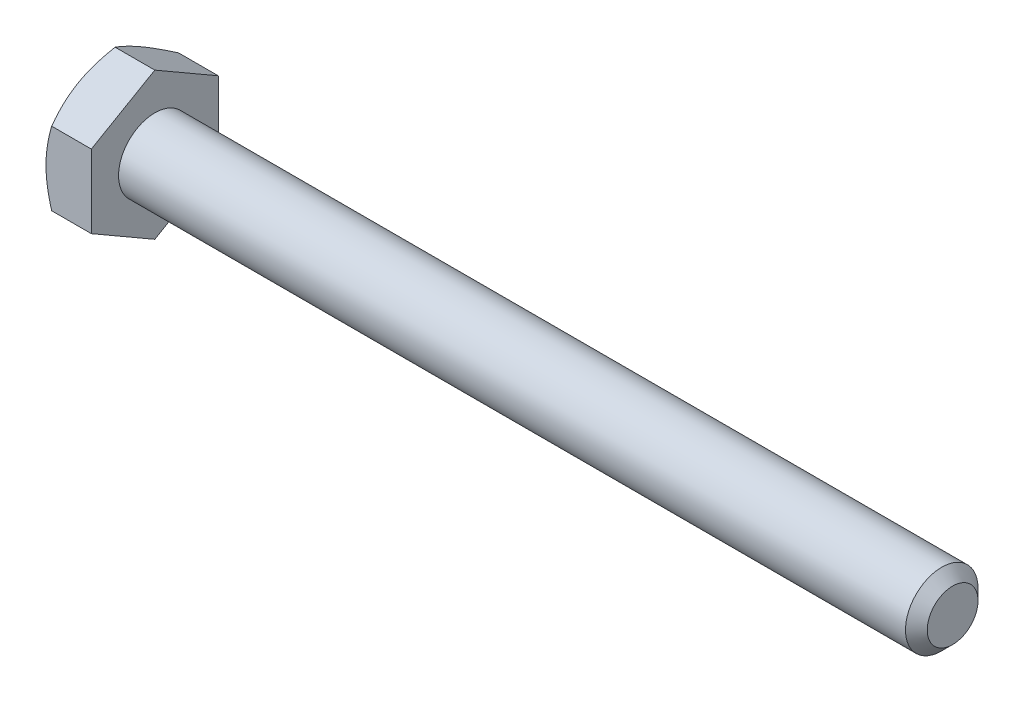
SolidWorks part; units mm, degrees
ref_plane "Front Plane" through (0, 0, 0) normal (0, 0, 1) x (1, 0, 0)
ref_plane "Top Plane" through (0, 0, 0) normal (0, 1, 0) x (1, 0, 0)
ref_plane "Right Plane" through (0, 0, 0) normal (1, 0, 0) x (0, 0, -1)
sketch "Sketch1" plane through (0, 0, 0) normal (0, 0, 1) x (1, 0, 0)
  line L0 (-36.9094, 0) -> (36.9094, 0) construction
  line L1 (36.9094, 3.175) -> (36.9094, -3.175) construction
  line L2 (-32.9406, 5.5562) -> (-32.9406, -5.5562) construction
  line L3 (-36.9094, 5.5562) -> (-36.9094, -5.5562) construction
  point P9 (-32.9406, 0)
  point P10 (32.4644, -3.175)
  dimension "D1" = 4.445
  dimension "Screw Dia" = 6.35
  dimension "Hex" = 11.1125
  dimension "Head Ht" = 3.9688
  dimension "Screw Lenght" = 69.85
ref_plane "Plane2" through (36.9094, 0, 0) normal (1, 0, 0) x (0, 0, -1)
sketch "Sketch5" plane through (36.9094, 0, 0) normal (1, 0, 0) x (0, 0, -1)
  circle A0 centre (0, 0) radius 3.175
extrude "Boss-Extrude3" add sketch "Sketch5" against normal up to vertex (69.85 mm away) up to point (-32.9406, 0, 0)
sketch "Sketch9" plane through (36.9094, 0, 0) normal (1, 0, 0) x (0, 0, -1)
  circle A1 centre (0, 0) radius 3.175
  circle A2 centre (0, 0) radius 3.175
  dimension "D1" = 0
curve "Helix/Spiral1" pitch 1.27 height 20.32 turns 16 parameters "Pitch"=1.27
chamfer "Chamfer1" distance 0.9525 angle 45 1 edges at (36.9094, 0, -3.175)
sketch "Sketch10" plane through (0, 0, 0) normal (0, 0, 1) x (1, 0, 0)
  line L0 (36.9094, 3.175) -> (37.3856, 2.3501)
  line L1 (37.3856, 2.3501) -> (37.5444, 2.3501)
  line L2 (37.5444, 2.3501) -> (38.0206, 3.175)
  line L3 (36.9094, 3.175) -> (38.0206, 3.175)
  line L4 (37.465, 3.175) -> (37.465, 2.3501) construction
  line L5 (37.1475, 2.7626) -> (37.7825, 2.7626) construction
  dimension "D1" = 60
  dimension "D2" = 0.1588
  dimension "D3" = 0.635
sketch "Sketch11" plane through (0, 0, 0) normal (0, 0, 1) x (1, 0, 0)
  line L0 (-32.9406, 3.175) -> (-32.9406, 0)
  line L1 (-32.9406, 0) -> (21.0344, 0)
  line L3 (21.0344, 0) -> (17.8594, 3.175)
  line L4 (-32.9406, 3.175) -> (17.8594, 3.175)
  dimension "D1" = 45
  dimension "MIn Thread" = 19.05
revolve "Revolve1" add sketch "Sketch11" angle 360 about L1
sketch "Sketch6" plane through (-32.9406, 0, 0) normal (-1, 0, 0) x (0, 0, 1)
  line L0 (0, 5.5562) -> (0, -5.5562) construction
  line L1 (5.5563, 3.2079) -> (0, 6.4158)
  line L2 (0, 6.4158) -> (-5.5562, 3.2079)
  line L3 (-5.5562, 3.2079) -> (-5.5562, -3.2079)
  line L4 (-5.5562, -3.2079) -> (0, -6.4158)
  line L5 (0, -6.4158) -> (5.5563, -3.2079)
  line L6 (5.5563, -3.2079) -> (5.5563, 3.2079)
  circle A0 centre (0, 0) radius 5.5563 construction
extrude "Boss-Extrude4" add sketch "Sketch6" along normal up to vertex (3.9688 mm away) up to point (-36.9094, -5.5562, 0)
sketch "Sketch7" plane through (-36.9094, 0, 0) normal (-1, 0, 0) x (0, 0, 1)
  circle A0 centre (0, 0) radius 5.5563 construction
  circle A1 centre (0, 0) radius 5.5563
sketch "Sketch8" plane through (-36.9094, 0, 0) normal (-1, 0, 0) x (0, 0, 1)
  circle A0 centre (0, 0) radius 5.5563 construction
  circle A1 centre (0, 0) radius 5.5563
extrude "Cut-Extrude3" cut sketch "Sketch8" against normal through all draft 60 flip side to cut
sketch "Sketch12" plane through (-36.9094, 0, 0) normal (-1, 0, 0) x (0, 0, 1)
  line L0 (0, 4.2783) -> (0, 2.3892) construction
  line L1 (0.1667, 4.2783) -> (0.1667, 2.3892)
  line L2 (-0.1667, 4.2783) -> (-0.1667, 2.3892)
  line L3 (0, 3.175) -> (0, -3.175) construction
  arc A0 (0.1667, 4.2783) -> (-0.1667, 4.2783) centre (0, 4.2783) ccw
  arc A1 (-0.1667, 2.3892) -> (0.1667, 2.3892) centre (0, 2.3892) ccw
  circle A3 centre (0, 0) radius 2.2225 construction
  circle A4 centre (0, 0) radius 4.445 construction
  point P2 (0, 3.3337)
  dimension "D1" = 4.445
  dimension "D3" = 8.89
  dimension "D2" = 0.3334
extrude "Cut-Extrude4" cut sketch "Sketch12" against normal blind 0.254
pattern_circular "CirPattern1" count 3 over 360 about axis through (0, 0, 0) along (1, 0, 0) of "Cut-Extrude4"
equation "\"D2@Sketch10\" = \"Pitch@Helix/Spiral1\"*.125"
equation "\"D3@Sketch10\" = \"Pitch@Helix/Spiral1\"*.5"
equation "\"D3@Helix/Spiral1\" = \"MIn Thread@Sketch11\"+\"Pitch@Helix/Spiral1\""
equation "\"D1@Chamfer1\" = \"Pitch@Helix/Spiral1\"*.75"
equation "\"D1@Sketch12\" = \"Hex@Sketch1\"*.4"
equation "\"D3@Sketch12\" = \"Hex@Sketch1\"*.8"
equation "\"D2@Sketch12\" = \"Hex@Sketch1\"*.03"
equation "\"D1@Sketch1\" = \"Pitch@Helix/Spiral1\"*3.5"
